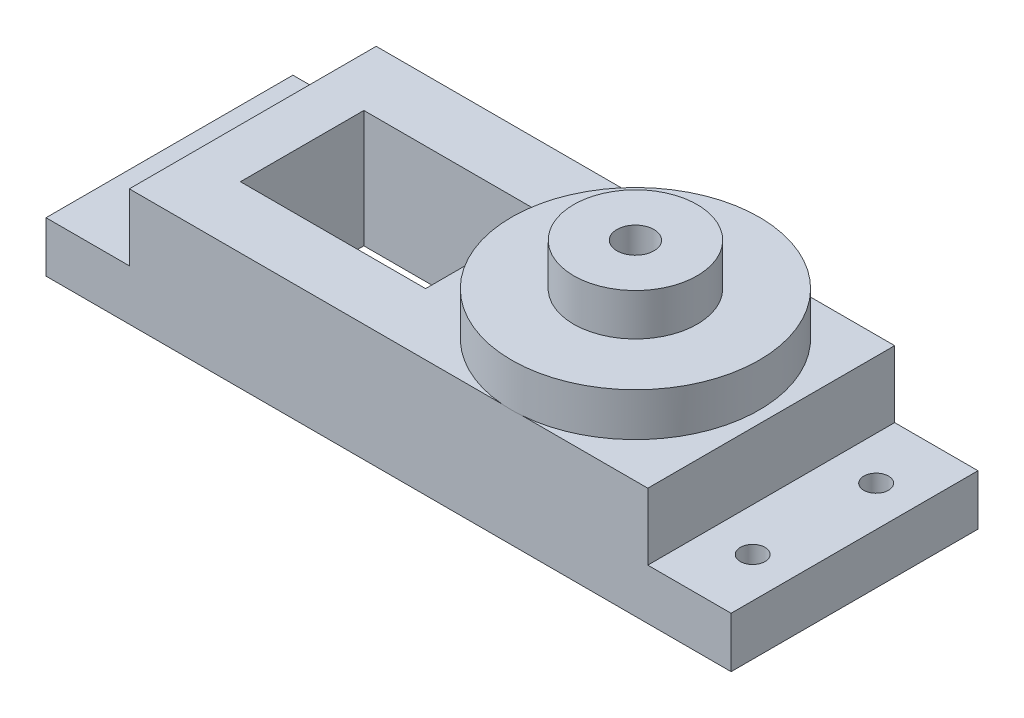
SolidWorks part; units mm, degrees
ref_plane "Alzado" through (0, 0, 0) normal (0, 0, 1) x (1, 0, 0)
ref_plane "Planta" through (0, 0, 0) normal (0, 1, 0) x (1, 0, 0)
ref_plane "Vista lateral" through (0, 0, 0) normal (1, 0, 0) x (0, 0, -1)
sketch "Croquis1" plane through (0, 0, 0) normal (0, 1, 0) x (1, 0, 0)
  line L0 (-28.2455, 9.8761) -> (27.2545, 9.8761)
  line L1 (-28.2455, 9.8761) -> (-28.2455, -10.1239)
  line L2 (-28.2455, -10.1239) -> (27.2545, -10.1239)
  line L3 (27.2545, 9.8761) -> (27.2545, -10.1239)
  line L4 (-17.4955, 4.8761) -> (-2.4955, 4.8761)
  line L5 (-17.4955, 4.8761) -> (-17.4955, -5.1239)
  line L6 (-17.4955, -5.1239) -> (-2.4955, -5.1239)
  line L7 (-2.4955, 4.8761) -> (-2.4955, -5.1239)
  circle A0 centre (-24.9955, 4.8761) radius 1
  circle A1 centre (-24.9955, -5.1239) radius 1
  circle A2 centre (9.5045, -0.1239) radius 1.5
  circle A3 centre (24.0045, 4.8761) radius 1
  circle A4 centre (24.0045, -5.1239) radius 1
extrude "Saliente-Extruir1" add sketch "Croquis1" along normal blind 4.1
sketch "Croquis2" plane through (0, 4.1, 0) normal (0, 1, 0) x (1, 0, 0)
  line L0 (27.2545, 9.8761) -> (-28.2455, 9.8761) construction
  line L1 (-21.4955, 9.8761) -> (20.5045, 9.8761)
  line L2 (-21.4955, 9.8761) -> (-21.4955, -10.1239)
  line L3 (-21.4955, -10.1239) -> (20.5045, -10.1239)
  line L4 (20.5045, 9.8761) -> (20.5045, -10.1239)
  line L5 (-28.2455, -10.1239) -> (27.2545, -10.1239) construction
  line L6 (-28.2455, 9.8761) -> (-28.2455, -10.1239) construction
  line L8 (-17.4955, 4.8761) -> (-2.4955, 4.8761)
  line L9 (-17.4955, 4.8761) -> (-17.4955, -5.1239)
  line L10 (-17.4955, -5.1239) -> (-2.4955, -5.1239)
  line L11 (-2.4955, 4.8761) -> (-2.4955, -5.1239)
  circle A0 centre (9.5045, -0.1239) radius 1.5 construction
  circle A1 centre (9.5045, -0.1239) radius 1.5
  dimension "D1" = 42
  dimension "D2" = 6.75
extrude "Saliente-Extruir2" add sketch "Croquis2" along normal blind 5.4
sketch "Croquis3" plane through (0, 9.5, 0) normal (0, 1, 0) x (1, 0, 0)
  circle A0 centre (9.5045, -0.1239) radius 1.5 construction
  circle A1 centre (9.5045, -0.1239) radius 1.5
  circle A2 centre (9.5045, -0.1239) radius 10.0332
extrude "Saliente-Extruir3" add sketch "Croquis3" along normal blind 3.5
sketch "Croquis4" plane through (0, 13, 0) normal (0, 1, 0) x (1, 0, 0)
  circle A0 centre (9.5045, -0.1239) radius 1.5 construction
  circle A1 centre (9.5045, -0.1239) radius 1.5
  circle A2 centre (9.5045, -0.1239) radius 5
  dimension "D1" = 10
extrude "Saliente-Extruir4" add sketch "Croquis4" along normal blind 3.4
